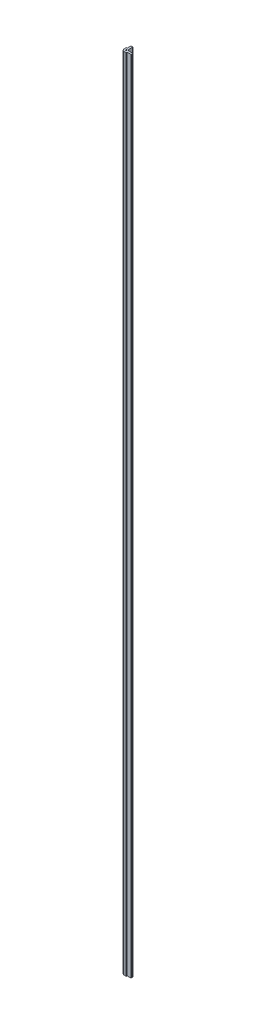
SolidWorks part; units mm, degrees
material "6063-T6"
ref_plane "Front" through (0, 0, 0) normal (0, 0, 1) x (1, 0, 0)
ref_plane "Top" through (0, 0, 0) normal (0, 1, 0) x (1, 0, 0)
ref_plane "Right" through (0, 0, 0) normal (1, 0, 0) x (0, 0, -1)
sketch "Sketch1" plane through (0, 0, 0) normal (0, 1, 0) x (1, 0, 0)
  line L0 (-3.048, 13.208) -> (-3.048, 4.953)
  line L1 (0, -5.08) -> (4.572, -5.08)
  line L2 (-5.08, 0) -> (-5.08, 4.572)
  line L3 (-2.286, 13.97) -> (0.508, 13.97)
  line L4 (13.97, -2.286) -> (13.97, 0.508)
  line L5 (13.208, -3.048) -> (4.953, -3.048)
  line L6 (4.826, -3.175) -> (4.826, -4.826)
  line L7 (-3.175, 4.826) -> (-4.826, 4.826)
  line L9 (1.27, 13.208) -> (1.27, 3.7674)
  line L10 (3.7674, 1.27) -> (13.208, 1.27)
  arc A0 (0, -5.08) -> (-5.08, 0) centre (0, 0) cw
  arc A1 (4.953, -3.048) -> (4.826, -3.175) centre (4.953, -3.175) ccw
  arc A2 (-3.048, 4.953) -> (-3.175, 4.826) centre (-3.175, 4.953) cw
  arc A7 (13.208, -3.048) -> (13.97, -2.286) centre (13.208, -2.286) ccw
  arc A8 (-3.048, 13.208) -> (-2.286, 13.97) centre (-2.286, 13.208) cw
  arc A9 (4.826, -4.826) -> (4.572, -5.08) centre (4.572, -4.826) cw
  arc A10 (-4.826, 4.826) -> (-5.08, 4.572) centre (-4.826, 4.572) ccw
  arc A11 (3.532, 1.4288) -> (1.4288, 3.532) centre (0, 0) ccw
  arc A12 (1.27, 13.208) -> (0.508, 13.97) centre (0.508, 13.208) ccw
  arc A13 (13.208, 1.27) -> (13.97, 0.508) centre (13.208, 0.508) cw
  arc A14 (1.4288, 3.532) -> (1.27, 3.7674) centre (1.524, 3.7674) cw
  arc A15 (3.532, 1.4288) -> (3.7674, 1.27) centre (3.7674, 1.524) ccw
  point P0 (0, 0)
  point P20 (-3.048, 4.826)
  point P28 (-5.08, 4.826)
  point P35 (-3.048, 13.97)
  dimension "D3" = 5.08
  dimension "D8" = 0.127
  dimension "D10" = 0.254
  dimension "D4" = 3.81
  dimension "D5" = 0.762
  dimension "D2" = 19.05
  dimension "D6" = 2.032
  dimension "D7" = 9.144
  dimension "D11" = 6.35
extrude "Boss-Extrude1" add sketch "Sketch1" along normal blind 1828.8
hole_wizard "THRU HOLES" positions "Sketch2" profile "Sketch3" hole size "#6-32" standard "ANSI Inch" end condition through all
sketch "Sketch2" plane through (0, 1828.8, 0) normal (0, 1, 0) x (1, 0, 0)
  point P0 (0, 0)
sketch "Sketch3" plane through (0, 1828.8, 0) normal (1, 0, 0) x (0, 0, 1)
  line L0 (0, 0) -> (0, 1828.8)
  line L1 (0, 1828.8) -> (1.397, 1828.8)
  line L2 (1.397, 1828.8) -> (1.397, 0)
  line L5 (1.397, 0) -> (0, 0)
  line L11 (0, -6.35) -> (0, 107.95) construction
  dimension "Thru Hole Dia." = 2.794
  dimension "Thru Hole Depth" = 1828.8
